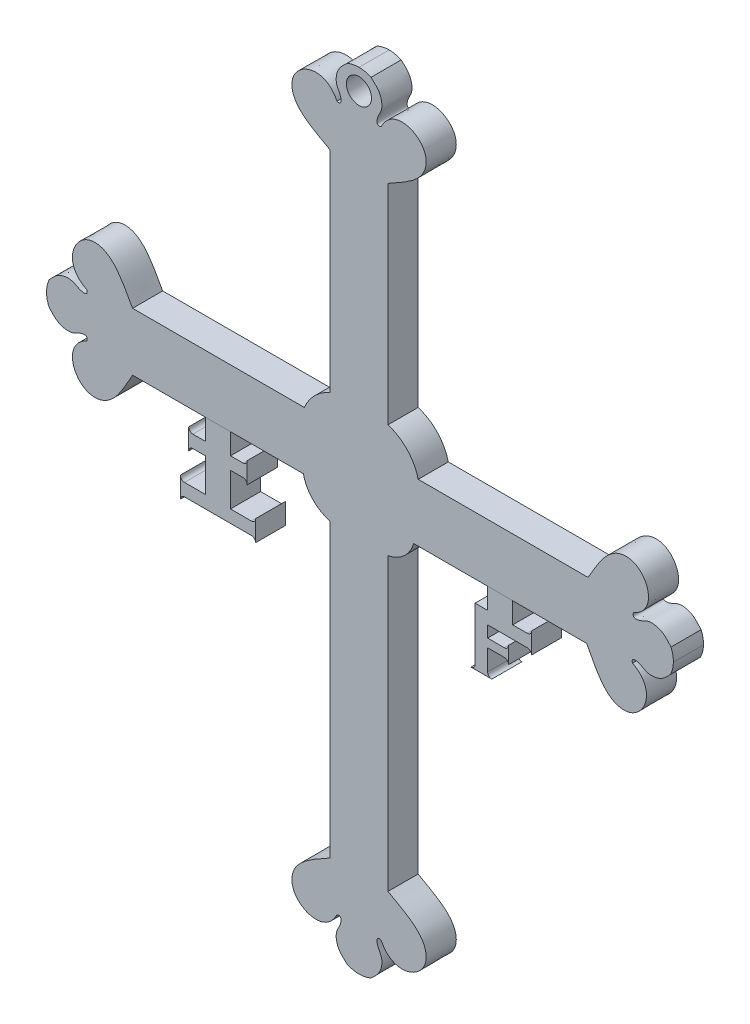
SolidWorks part; units mm, degrees
ref_plane "Alzado" through (0, 0, 0) normal (0, 0, 1) x (1, 0, 0)
ref_plane "Planta" through (0, 0, 0) normal (0, 1, 0) x (1, 0, 0)
ref_plane "Vista lateral" through (0, 0, 0) normal (1, 0, 0) x (0, 0, -1)
sketch "Croquis1" plane through (0, 0, 0) normal (0, 0, 1) x (1, 0, 0)
  line L0 (-363.8339, 123.8944) -> (-30.5006, 123.8944) construction
  line L1 (-250.9984, 164.7424) -> (-250.9984, 114.5106)
  line L2 (-237.1616, 164.7424) -> (-237.1616, 114.7424)
  line L3 (-243.8551, 101.1993) -> (-243.7348, 111.5516) construction
  line L4 (-250.9984, 164.7424) -> (-237.1616, 164.7424) construction
  line L5 (-318.7128, 186.4387) -> (-168.7128, -3.5613) construction
  line L6 (-318.7128, -3.5613) -> (-168.7128, 186.4387) construction
  line L7 (-244.08, 164.7424) -> (-244.08, 185.3129) construction
  line L8 (-189.3337, 107.077) -> (-189.6553, 93.244) construction
  line L9 (-189.4945, 100.1605) -> (-168.9295, 99.6824) construction
  line L10 (-189.6553, 93.244) -> (-231.0126, 93.244)
  line L11 (-189.3337, 107.077) -> (-229.9386, 107.077)
  line L12 (-244.1625, 86.0955) -> (-259.9815, 86.0955) construction
  line L13 (-243.9913, 94.5058) -> (-251.5857, 94.5058) construction
  line L14 (-243.7128, 91.4387) -> (-250.9984, 91.4387) construction
  line L15 (-244.08, 18.135) -> (-244.08, -2.4355) construction
  line L16 (-298.2252, 94.5058) -> (-257.3982, 94.5058)
  line L17 (-298.2252, 101.1993) -> (-180.312, 101.4242) construction
  line L18 (-243.5477, 116.303) -> (-244.1625, 86.0955) construction
  line L19 (-180.312, 108.3426) -> (-287.312, 108.3426) construction
  line L20 (-307.3982, 94.056) -> (-307.3982, 107.8928) construction
  line L21 (-307.3982, 100.9744) -> (-327.9687, 100.9744) construction
  line L22 (-250.9984, 18.135) -> (-237.1616, 18.135) construction
  line L23 (-307.3982, 107.8928) -> (-257.3982, 107.8928) [skipped]
  line L24 (-287.312, 108.3426) -> (-233.812, 108.3426) construction
  line L25 (-233.812, 108.3426) -> (-233.812, 89.9141) construction
  line L26 (-239.2686, 101.3117) -> (-239.2686, 86.8055) construction
  line L27 (-298.2252, 101.4242) -> (-318.7958, 101.4242) construction
  line L28 (-298.2252, 108.3426) -> (-298.2252, 94.5058) construction
  line L29 (-298.2252, 108.3426) -> (-257.1665, 108.3426)
  line L30 (-180.312, 108.3426) -> (-180.312, 94.5058) construction
  line L31 (-180.312, 101.4242) -> (-159.7415, 101.4242) construction
  line L32 (-180.312, 94.5058) -> (-230.312, 94.5058) [skipped]
  line L33 (-250.9984, 18.135) -> (-250.9984, 87.888)
  line L34 (-236.7119, 37.6562) -> (-250.5486, 37.6562) construction
  line L35 (-243.6302, 37.6562) -> (-243.6302, 17.0857) construction
  line L36 (-250.5486, 37.6562) -> (-250.5486, 87.6562) [skipped]
  line L37 (-237.1616, 18.135) -> (-237.1616, 87.6562)
  arc A0 (-257.1665, 108.3426) -> (-250.9984, 114.5106) centre (-246.4666, 103.8108) cw
  arc A1 (-237.1616, 114.7424) -> (-229.9386, 107.077) centre (-240.2666, 104.5808) cw
  arc A2 (-257.3982, 94.5058) -> (-250.9984, 87.888) centre (-248.8277, 96.3905) ccw
  arc A3 (-237.1616, 87.6562) -> (-231.0126, 93.244) centre (-238.6457, 95.4666) ccw
  spline S0 degree 3 poles (-250.9984, 164.7424) (-253.872, 166.4695) (-260.1017, 169.0667) (-260.254, 178.5935) (-252.1891, 181.4893) (-249.3689, 175.6583) knots 0 0 0 0 0.445418 0.535608 1 1 1 1
  spline S1 degree 3 poles (-237.1616, 164.7424) (-234.288, 166.4695) (-228.0583, 169.0667) (-227.906, 178.5935) (-235.9709, 181.4893) (-238.7911, 175.6583) knots 0 0 0 0 0.445418 0.535608 1 1 1 1
  spline S2 degree 3 poles (-249.3689, 175.6583) (-248.1254, 175.2612) (-248.3902, 177.3738) (-249.6384, 179.0551) (-249.5743, 181.2866) (-248.5877, 183.2614) (-247.5015, 184.1496) (-246.9598, 184.6861) knots 0 0 0 0 0.226165 0.394336 0.620843 0.785939 1 1 1 1
  spline S3 degree 2 poles (-246.9598, 184.6861) (-245.5194, 185.3179) (-244.08, 185.3129) knots 0 0 0 0.504568 0.504568 0.504568
  spline S4 degree 2 poles (-241.2002, 184.6861) (-242.6406, 185.3179) (-244.08, 185.3129) knots 0 0 0 0.504568 0.504568 0.504568
  spline S5 degree 3 poles (-238.7911, 175.6583) (-240.0346, 175.2612) (-239.7698, 177.3738) (-238.5216, 179.0551) (-238.5857, 181.2866) (-239.5724, 183.2614) (-240.6585, 184.1496) (-241.2002, 184.6861) knots 0 0 0 0 0.226165 0.394336 0.620843 0.785939 1 1 1 1
  spline S6 degree 3 poles (-189.3337, 107.077) (-187.5402, 109.9097) (-184.799, 116.0774) (-175.2712, 116.0082) (-172.5636, 107.8782) (-178.4586, 105.1942) knots 0 0 0 0 0.445418 0.535608 1 1 1 1
  spline S7 degree 3 poles (-189.6553, 93.244) (-187.9954, 90.331) (-185.5437, 84.0426) (-176.023, 83.669) (-172.9405, 91.6644) (-178.7044, 94.6194) knots 0 0 0 0 0.445418 0.535608 1 1 1 1
  spline S8 degree 3 poles (-178.4586, 105.1942) (-178.8844, 103.9604) (-176.7663, 104.176) (-175.0564, 105.3848) (-172.827, 105.2688) (-170.8757, 104.2365) (-170.013, 103.1301) (-169.4892, 102.576) knots 0 0 0 0 0.226165 0.394336 0.620843 0.785939 1 1 1 1
  spline S9 degree 2 poles (-169.4892, 102.576) (-168.891, 101.1213) (-168.9295, 99.6824) knots 0 0 0 0.504568 0.504568 0.504568
  spline S10 degree 2 poles (-169.6231, 96.818) (-168.9579, 98.2433) (-168.9295, 99.6824) knots 0 0 0 0.504568 0.504568 0.504568
  spline S11 degree 3 poles (-178.7044, 94.6194) (-179.0725, 95.8717) (-176.9667, 95.5579) (-175.3148, 94.2709) (-173.0824, 94.2832) (-171.0852, 95.2237) (-170.172, 96.2889) (-169.6231, 96.818) knots 0 0 0 0 0.226165 0.394336 0.620843 0.785939 1 1 1 1
  spline S12 degree 3 poles (-238.7911, 7.219) (-240.0346, 7.6161) (-239.7698, 5.5036) (-238.5216, 3.8223) (-238.5857, 1.5907) (-239.5724, -0.384) (-240.6585, -1.2723) (-241.2002, -1.8087) knots 0 0 0 0 0.226165 0.394336 0.620843 0.785939 1 1 1 1
  spline S13 degree 2 poles (-241.2002, -1.8087) (-242.6406, -2.4406) (-244.08, -2.4355) knots 0 0 0 0.504568 0.504568 0.504568
  spline S14 degree 2 poles (-246.9598, -1.8087) (-245.5194, -2.4406) (-244.08, -2.4355) knots 0 0 0 0.504568 0.504568 0.504568
  spline S15 degree 3 poles (-249.3689, 7.219) (-248.1254, 7.6161) (-248.3902, 5.5036) (-249.6384, 3.8223) (-249.5743, 1.5907) (-248.5877, -0.384) (-247.5015, -1.2723) (-246.9598, -1.8087) knots 0 0 0 0 0.226165 0.394336 0.620843 0.785939 1 1 1 1
  spline S16 degree 3 poles (-237.1616, 18.135) (-234.288, 16.4078) (-228.0583, 13.8107) (-227.906, 4.2839) (-235.9709, 1.3881) (-238.7911, 7.219) knots 0 0 0 0 0.445418 0.535608 1 1 1 1
  spline S17 degree 3 poles (-250.9984, 18.135) (-253.872, 16.4078) (-260.1017, 13.8107) (-260.254, 4.2839) (-252.1891, 1.3881) (-249.3689, 7.219) knots 0 0 0 0 0.445418 0.535608 1 1 1 1
  spline S18 degree 3 poles (-309.1412, 96.1353) (-308.7441, 97.3787) (-310.8566, 97.114) (-312.538, 95.8658) (-314.7695, 95.9299) (-316.7442, 96.9165) (-317.6325, 98.0026) (-318.1689, 98.5444) knots 0 0 0 0 0.226165 0.394336 0.620843 0.785939 1 1 1 1
  spline S19 degree 2 poles (-318.1689, 98.5444) (-318.8008, 99.9848) (-318.7958, 101.4242) knots 0 0 0 0.504568 0.504568 0.504568
  spline S20 degree 2 poles (-318.1689, 104.304) (-318.8008, 102.8636) (-318.7958, 101.4242) knots 0 0 0 0.504568 0.504568 0.504568
  spline S21 degree 3 poles (-309.1412, 106.713) (-308.7441, 105.4696) (-310.8566, 105.7344) (-312.538, 106.9826) (-314.7695, 106.9185) (-316.7442, 105.9318) (-317.6325, 104.8457) (-318.1689, 104.304) knots 0 0 0 0 0.226165 0.394336 0.620843 0.785939 1 1 1 1
  spline S22 degree 3 poles (-298.2252, 94.5058) (-299.9524, 91.6322) (-302.5496, 85.4025) (-312.0764, 85.2502) (-314.9721, 93.3151) (-309.1412, 96.1353) knots 0 0 0 0 0.445418 0.535608 1 1 1 1
  spline S23 degree 3 poles (-298.2252, 108.3426) (-299.9524, 111.2162) (-302.5496, 117.4459) (-312.0764, 117.5982) (-314.9721, 109.5332) (-309.1412, 106.713) knots 0 0 0 0 0.445418 0.535608 1 1 1 1
  point P0 (-243.7128, 91.4387)
  point P139 (-243.8551, 101.1993)
  dimension "D1" = 150
  dimension "D2" = 190
  dimension "D3" = 41.0588
  dimension "D4" = 4
  dimension "D6" = 0.5
extrude "Saliente-Extruir1" add sketch "Croquis1" along normal blind 7.2
sketch "Croquis2" plane through (0, 0, 7.2) normal (0, 0, 1) x (1, 0, 0)
  line L0 (-298.2252, 94.5058) -> (-257.3982, 94.5058) construction
  line L1 (-283.8117, 89.5058) -> (-283.8117, 90.5058) construction
  line L2 (-280.8117, 94.5058) -> (-280.8117, 89.5058)
  line L3 (-280.8117, 89.5058) -> (-283.8117, 89.5058)
  line L4 (-284.8117, 90.5058) -> (-284.8117, 85.5058)
  line L5 (-283.8117, 86.5058) -> (-280.8117, 86.5058)
  line L6 (-280.8117, 86.5058) -> (-280.8117, 78.5058)
  line L7 (-280.8117, 78.5058) -> (-285.8117, 78.5058)
  line L8 (-286.8117, 79.5058) -> (-286.8117, 74.5058)
  line L9 (-285.8117, 75.5058) -> (-269.8117, 75.5058)
  line L10 (-216.3339, 75.5058) -> (-217.3339, 75.5058) construction
  line L11 (-269.8117, 78.5058) -> (-274.8117, 78.5058)
  line L12 (-274.8117, 78.5058) -> (-274.8117, 86.5058)
  line L13 (-274.8117, 86.5058) -> (-271.8117, 86.5058)
  line L14 (-270.8117, 90.5058) -> (-270.8117, 85.5058)
  line L15 (-271.8117, 89.5058) -> (-274.8117, 89.5058)
  line L16 (-274.8117, 89.5058) -> (-274.8117, 94.5058)
  line L17 (-231.0126, 93.244) -> (-189.6553, 93.244) construction
  line L18 (-210.3339, 93.244) -> (-213.3339, 93.244)
  line L19 (-213.3339, 93.244) -> (-213.3339, 88.244)
  line L20 (-213.3339, 88.244) -> (-216.3339, 88.244)
  line L21 (-216.3339, 88.244) -> (-216.3339, 75.5058)
  line L22 (-208.3339, 83.5058) -> (-208.3339, 79.5058)
  line L23 (-213.3339, 75.5058) -> (-213.3339, 80.5058)
  line L24 (-213.3339, 80.5058) -> (-209.3339, 80.5058)
  line L25 (-209.3339, 82.5058) -> (-209.3339, 83.5058) construction
  line L26 (-209.3339, 83.5058) -> (-208.3339, 83.5058) construction
  line L27 (-213.3339, 83.5058) -> (-213.3339, 85.2458)
  line L28 (-213.3339, 85.2458) -> (-203.8348, 85.2458)
  line L30 (-203.8348, 88.244) -> (-207.3348, 88.244)
  line L31 (-207.3348, 88.244) -> (-207.3348, 93.244)
  line L32 (-207.3348, 93.244) -> (-213.3339, 93.244)
  line L33 (-280.8117, 94.5058) -> (-274.8117, 94.5058)
  line L34 (-283.8117, 90.5058) -> (-284.8117, 90.5058) construction
  line L35 (-284.8117, 90.5058) -> (-284.8117, 85.5058) construction
  line L36 (-284.8117, 85.5058) -> (-283.8117, 85.5058) construction
  line L37 (-283.8117, 85.5058) -> (-283.8117, 86.5058) construction
  line L38 (-285.8117, 78.5058) -> (-285.8117, 79.5058) construction
  line L39 (-285.8117, 79.5058) -> (-286.8117, 79.5058) construction
  line L40 (-286.8117, 79.5058) -> (-286.8117, 74.5058) construction
  line L41 (-286.8117, 74.5058) -> (-285.8117, 74.5058) construction
  line L42 (-285.8117, 74.5058) -> (-285.8117, 75.5058) construction
  line L43 (-271.8117, 89.5058) -> (-271.8117, 90.5058) construction
  line L44 (-271.8117, 90.5058) -> (-270.8117, 90.5058) construction
  line L45 (-270.8117, 90.5058) -> (-270.8117, 85.5058) construction
  line L46 (-270.8117, 85.5058) -> (-271.8117, 85.5058) construction
  line L47 (-271.8117, 85.5058) -> (-271.8117, 86.5058) construction
  line L48 (-269.8117, 78.5058) -> (-269.8117, 79.5058) construction
  line L49 (-269.8117, 79.5058) -> (-268.8117, 79.5058) construction
  line L50 (-268.8117, 79.5058) -> (-268.8117, 74.5058) construction
  line L51 (-268.8117, 74.5058) -> (-269.8117, 74.5058) construction
  line L52 (-269.8117, 74.5058) -> (-269.8117, 75.5058) construction
  line L53 (-268.8117, 79.5058) -> (-268.8117, 74.5058)
  line L54 (-217.3339, 75.5058) -> (-217.3339, 74.5058) construction
  line L55 (-217.3339, 74.5058) -> (-212.3339, 74.5058) construction
  line L56 (-212.3339, 74.5058) -> (-212.3339, 75.5058) construction
  line L57 (-212.3339, 75.5058) -> (-213.3339, 75.5058) construction
  line L58 (-217.3339, 74.5058) -> (-212.3339, 74.5058)
  line L59 (-209.3339, 82.5058) -> (-213.3339, 82.5058)
  line L60 (-213.3339, 82.5058) -> (-213.3339, 83.5058)
  line L61 (-208.3339, 83.5058) -> (-208.3339, 79.5058) construction
  line L62 (-208.3339, 79.5058) -> (-209.3339, 79.5058) construction
  line L63 (-209.3339, 79.5058) -> (-209.3339, 80.5058) construction
  line L64 (-203.8348, 88.244) -> (-203.8348, 89.2449) construction
  line L65 (-203.8348, 89.2449) -> (-202.8339, 89.2449) construction
  line L66 (-202.8339, 89.2449) -> (-202.8339, 84.2449) construction
  line L67 (-202.8339, 84.2449) -> (-203.8348, 84.2449) construction
  line L68 (-203.8348, 84.2449) -> (-203.8348, 85.2458) construction
  line L69 (-202.8339, 89.2449) -> (-202.8339, 84.2449)
  arc A0 (-284.8117, 85.5058) -> (-283.8117, 86.5058) centre (-283.8117, 85.5058) cw
  arc A1 (-283.8117, 89.5058) -> (-284.8117, 90.5058) centre (-283.8117, 90.5058) cw
  arc A2 (-285.8117, 78.5058) -> (-286.8117, 79.5058) centre (-285.8117, 79.5058) cw
  arc A3 (-285.8117, 75.5058) -> (-286.8117, 74.5058) centre (-285.8117, 74.5058) ccw
  arc A4 (-271.8117, 89.5058) -> (-270.8117, 90.5058) centre (-271.8117, 90.5058) ccw
  arc A5 (-271.8117, 86.5058) -> (-270.8117, 85.5058) centre (-271.8117, 85.5058) cw
  arc A6 (-269.8117, 75.5058) -> (-268.8117, 74.5058) centre (-269.8117, 74.5058) cw
  arc A7 (-269.8117, 78.5058) -> (-268.8117, 79.5058) centre (-269.8117, 79.5058) ccw
  arc A8 (-216.3339, 75.5058) -> (-217.3339, 74.5058) centre (-217.3339, 75.5058) cw
  arc A9 (-213.3339, 75.5058) -> (-212.3339, 74.5058) centre (-212.3339, 75.5058) ccw
  arc A10 (-209.3339, 80.5058) -> (-208.3339, 79.5058) centre (-209.3339, 79.5058) cw
  arc A11 (-209.3339, 82.5058) -> (-208.3339, 83.5058) centre (-209.3339, 83.5058) ccw
  arc A12 (-203.8348, 88.244) -> (-202.8339, 89.2449) centre (-203.8348, 89.2449) ccw
  arc A13 (-203.8348, 85.2458) -> (-202.8339, 84.2449) centre (-203.8348, 84.2449) cw
  line M26 (-298.2252, 94.5058) -> (-257.3982, 94.5058)
extrude "Saliente-Extruir2" add sketch "Croquis2" against normal up to vertex (7.2 mm away) separate body contours A7 L11 L12 L13 A5 L14 A4 L15 L16 L2 L3 A1 L4 A0 L5 L6 L7 A2 L8 A3 L9 A6 L53 M26 | L19 L20 L21 A8 L58 A9 L23 L24 A10 L22 A11 L59 L60 L27 L28 A13 L69 A12 L30 L31 L32
sketch "Croquis3" plane through (0, 0, 7.2) normal (0, 0, 1) x (1, 0, 0)
  circle A0 centre (-244.1023, 180.3929) radius 3
extrude "Cortar-Extruir1" cut sketch "Croquis3" against normal up to vertex (7.2 mm away)
